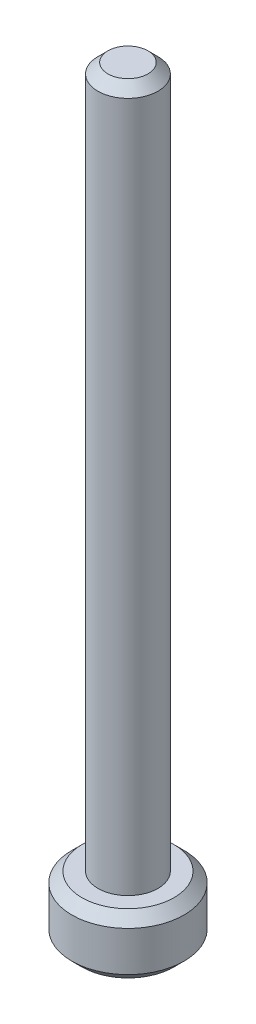
SolidWorks part; units mm, degrees
material "Zinc AC43A (Zn-4Al-2.5Cu-0.04Mg; Number 2 Die Casting Alloy; Zamak 2), Die Cast"
ref_plane "Plano frontal" through (0, 0, 0) normal (0, 0, 1) x (1, 0, 0)
ref_plane "Plano superior" through (0, 0, 0) normal (0, 1, 0) x (1, 0, 0)
ref_plane "Plano direito" through (0, 0, 0) normal (1, 0, 0) x (0, 0, -1)
sketch "Sketch1" plane through (0, 0, 0) normal (0, 1, 0) x (1, 0, 0)
  circle A0 centre (0, 0) radius 2.8
  dimension "D1" = 5.6
extrude "Boss-Extrude1" add sketch "Sketch1" along normal mid plane 3
sketch "Sketch2" plane through (0, 1.5, 0) normal (0, 1, 0) x (1, 0, 0)
  circle A0 centre (0, 0) radius 1.5
  dimension "D1" = 3
extrude "Boss-Extrude2" add sketch "Sketch2" along normal blind 35
chamfer "Chamfer1" distance 0.5 angle 45 1 edges at (0, 36.5, 1.5)
chamfer "Chamfer2" distance 0.5 angle 45 2 edges at (0, 1.5, 2.8) (0, -1.5, 2.8)
